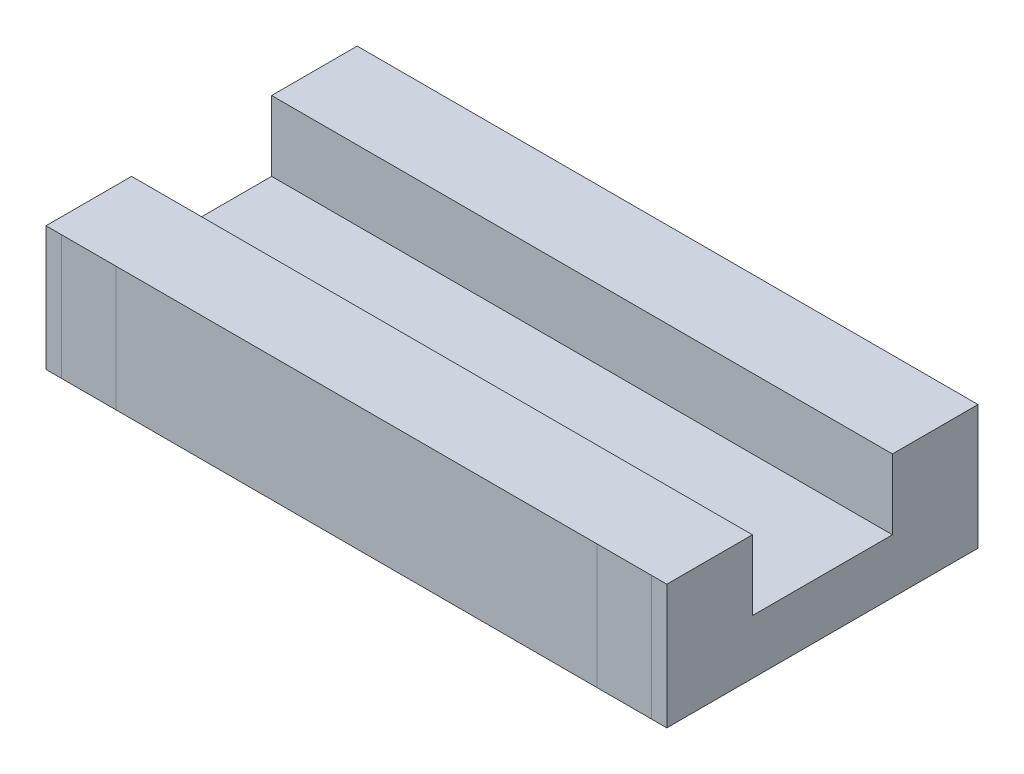
SolidWorks part; units mm, degrees
material "合金钢"
ref_plane "前视基准面" through (0, 0, 0) normal (0, 0, 1) x (1, 0, 0)
ref_plane "上视基准面" through (0, 0, 0) normal (0, 1, 0) x (1, 0, 0)
ref_plane "右视基准面" through (0, 0, 0) normal (1, 0, 0) x (0, 0, -1)
sketch "草图1" plane through (0, 0, 0) normal (0, 1, 0) x (1, 0, 0)
  line L1 (-19.95, -10) -> (19.95, -10)
  line L2 (-19.95, -10) -> (-19.95, 10)
  line L3 (-19.95, 10) -> (19.95, 10)
  line L4 (19.95, -10) -> (19.95, 10)
  line L5 (-19.95, -10) -> (19.95, 10) construction
  line L6 (-19.95, 10) -> (19.95, -10) construction
  point P0 (0, 0)
  dimension "D1" = 39.9
  dimension "D2" = 20
extrude "凸台-拉伸1" add sketch "草图1" along normal blind 8
sketch "草图2" plane through (0, 8, 0) normal (0, 1, 0) x (1, 0, 0)
  line L0 (19.95, -10) -> (19.95, 10) construction
  line L1 (-19.95, -4.5) -> (19.95, -4.5)
  line L2 (-19.95, -4.5) -> (-19.95, 4.5)
  line L3 (-19.95, 4.5) -> (19.95, 4.5)
  line L4 (19.95, -4.5) -> (19.95, 4.5)
  line L5 (-19.95, -4.5) -> (19.95, 4.5) construction
  line L6 (-19.95, 4.5) -> (19.95, -4.5) construction
  point P0 (0, 0)
  dimension "D1" = 9
extrude "切除-拉伸1" cut sketch "草图2" against normal blind 4.5
sketch "草图3" plane through (0, 0, 0) normal (0, -1, 0) x (1, 0, 0)
  line L0 (-19.95, 0) -> (19.95, 0) construction
  line L1 (-19.95, -10) -> (-19.95, 10) construction
  line L2 (19.95, 10) -> (19.95, -10) construction
  line L3 (0, 10) -> (0, -10) construction
  line L4 (-19.95, 10) -> (19.95, 10) construction
  line L5 (19.95, -10) -> (-19.95, -10) construction
  circle A0 centre (-8, 7.5) radius 1.5
  circle A1 centre (8, 7.5) radius 1.5
  circle A2 centre (8, -7.5) radius 1.5
  circle A3 centre (-8, -7.5) radius 1.5
  dimension "D1" = 3
  dimension "D2" = 16
  dimension "D3" = 15
extrude "切除-拉伸2" cut sketch "草图3" against normal blind 4
sketch "草图4" plane through (0, 0, 0) normal (0, -1, 0) x (1, 0, 0)
  line L0 (0, 10) -> (0, -10) construction
  line L1 (-19.95, 10) -> (19.95, 10) construction
  line L2 (19.95, -10) -> (-19.95, -10) construction
  line L3 (18.95, 10) -> (18.95, -10)
  line L4 (15.45, -10) -> (15.45, 10)
  line L5 (19.95, 10) -> (19.95, -10) construction
  line L6 (-15.45, -10) -> (-15.45, 10)
  line L7 (-18.95, 10) -> (-18.95, -10)
  dimension "D1" = 1
  dimension "D2" = 3.5
split line "分割线1"
